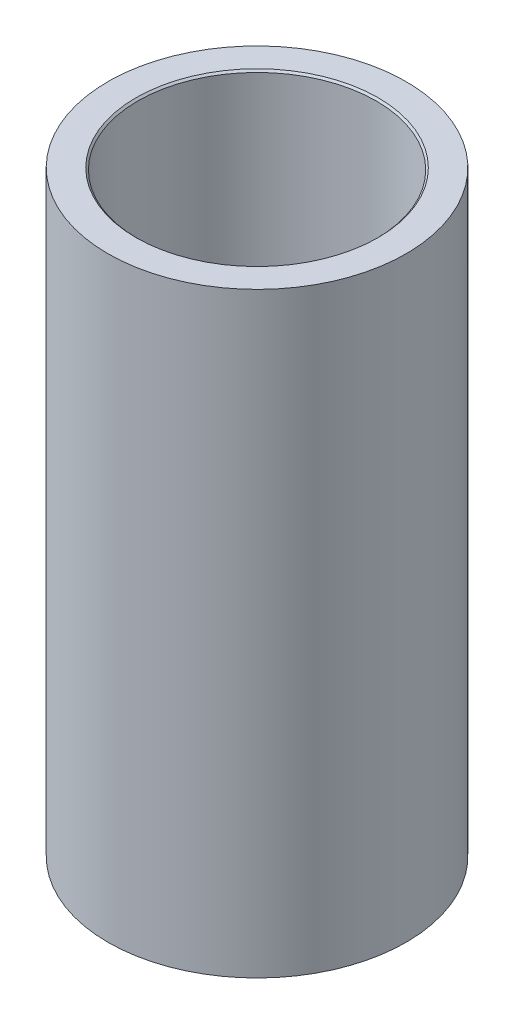
SolidWorks part; units mm, degrees
material "Laiton"
ref_plane "Plan de face" through (0, 0, 0) normal (0, 0, 1) x (1, 0, 0)
ref_plane "Plan de dessus" through (0, 0, 0) normal (0, 1, 0) x (1, 0, 0)
ref_plane "Plan de droite" through (0, 0, 0) normal (1, 0, 0) x (0, 0, -1)
sketch "Esquisse1" plane through (0, 0, 0) normal (0, 1, 0) x (1, 0, 0)
  circle A0 centre (0, 0) radius 2
  dimension "D1" = 4
extrude "Boss.-Extru.1" add sketch "Esquisse1" along normal blind 8
hole_wizard "Dégagement M32" positions "Esquisse11" profile "Esquisse12" hole size "M3" standard "Ansi Metric" end condition up to next
sketch "Esquisse11" plane through (0, 8, 0) normal (0, 1, 0) x (1, 0, 0)
  point P0 (0, 0)
sketch "Esquisse12" plane through (0, 8, 0) normal (1, 0, 0) x (0, 0, 1)
  line L0 (0, 0) -> (0, 8)
  line L1 (0, 8) -> (1.6, 8)
  line L2 (1.6, 8) -> (1.6, 0.025)
  line L3 (1.6, 0.025) -> (1.625, 0)
  line L5 (1.625, 0) -> (0, 0)
  line L6 (-1.6, 0.025) -> (-1.625, 0) construction
  line L11 (0, -6.35) -> (0, 107.95) construction
  dimension "Diamètre du perçage jusqu'au prochain" = 3.2
  dimension "Profondeur du perçage jusqu'au prochain" = 8
  dimension "Diamètre du fraisage entrant" = 3.25
  dimension "Angle du fraisage entrant" = 90
